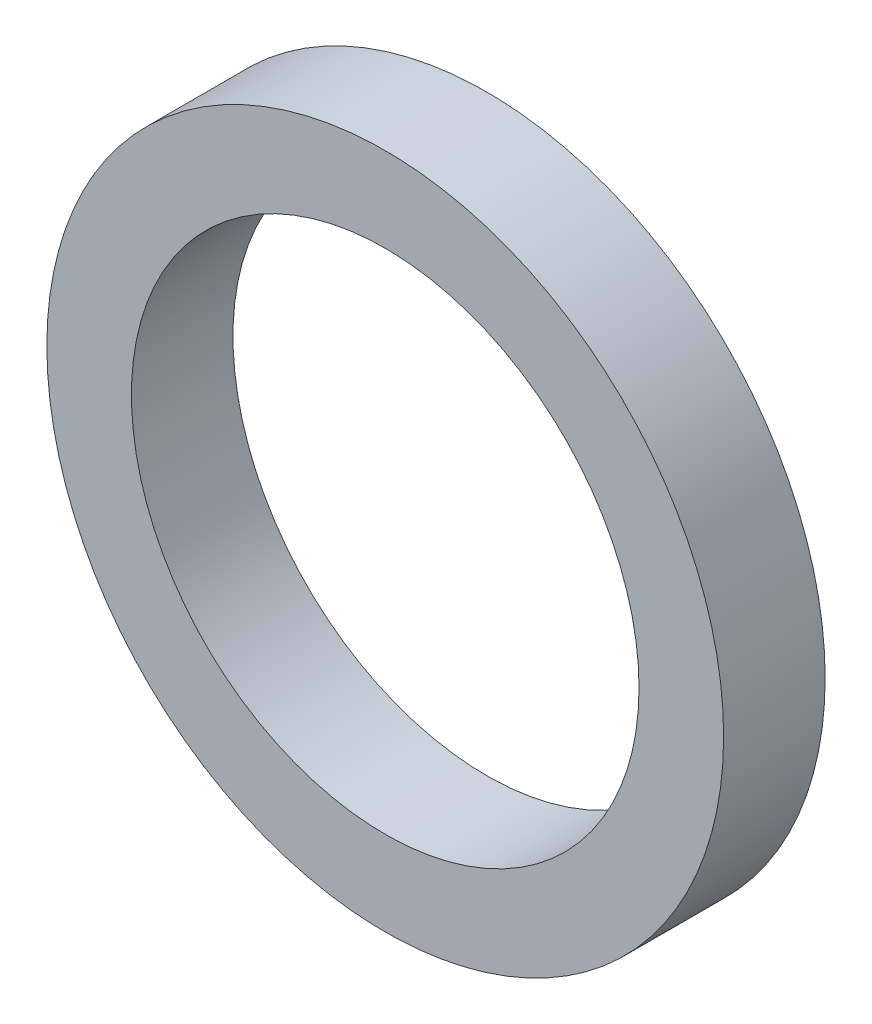
SolidWorks part; units mm, degrees
ref_plane "前视基准面" through (0, 0, 0) normal (0, 0, 1) x (1, 0, 0)
ref_plane "上视基准面" through (0, 0, 0) normal (0, 1, 0) x (1, 0, 0)
ref_plane "右视基准面" through (0, 0, 0) normal (1, 0, 0) x (0, 0, -1)
sketch "草图1" plane through (0, 0, 0) normal (0, 0, 1) x (1, 0, 0)
  circle A0 centre (0, 0) radius 4
  circle A1 centre (0, 0) radius 3
  dimension "D1" = 8
  dimension "D2" = 6
extrude "凸台-拉伸1" add sketch "草图1" along normal blind 1.2
